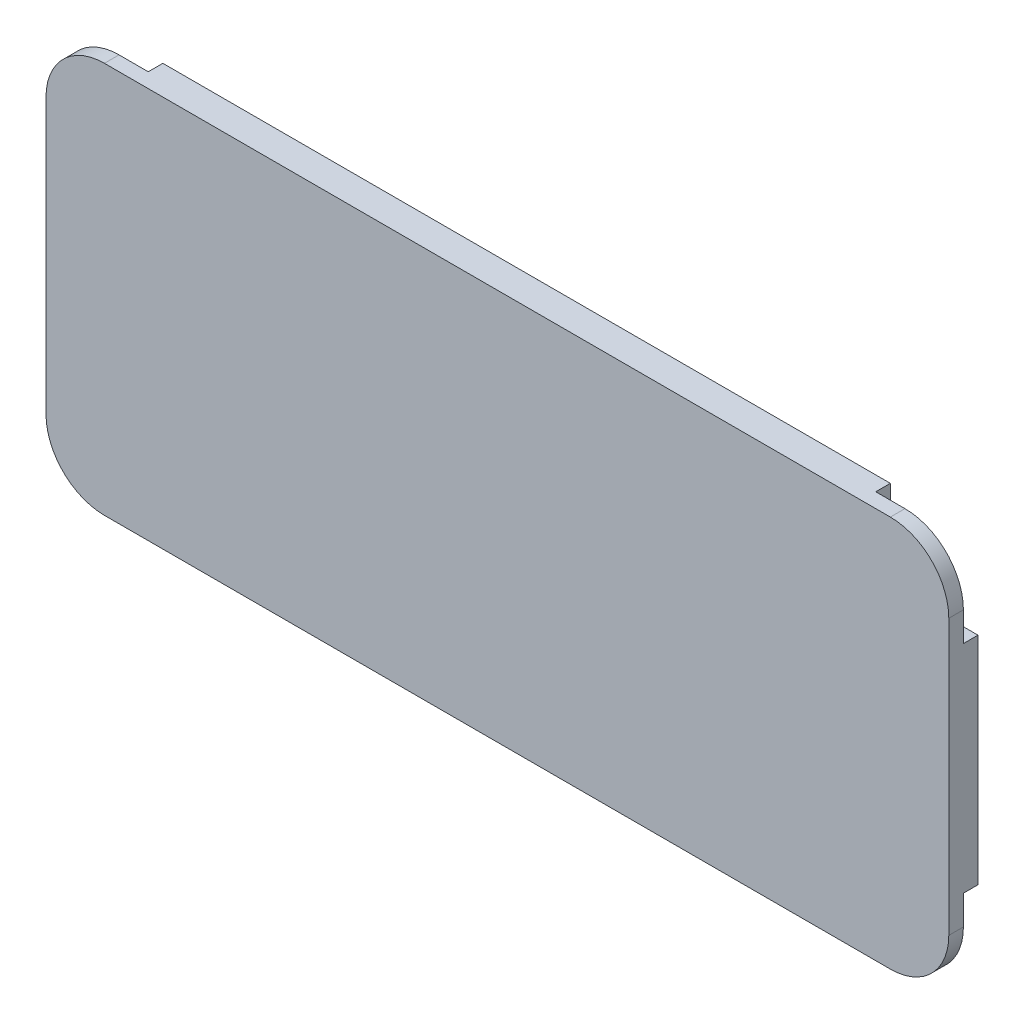
SolidWorks part; units mm, degrees
ref_plane "Front" through (0, 0, 0) normal (0, 0, 1) x (1, 0, 0)
ref_plane "Top" through (0, 0, 0) normal (0, 1, 0) x (1, 0, 0)
ref_plane "Right" through (0, 0, 0) normal (1, 0, 0) x (0, 0, -1)
sketch "草图1" plane through (0, 0, 0) normal (0, 0, 1) x (1, 0, 0)
  line L1 (2, 0) -> (28.9, 0)
  line L2 (0, 2) -> (0, 11.4)
  line L3 (2, 13.4) -> (28.9, 13.4)
  line L4 (30.9, 2) -> (30.9, 11.4)
  arc A0 (0, 11.4) -> (2, 13.4) centre (2, 11.4) cw
  arc A1 (28.9, 13.4) -> (30.9, 11.4) centre (28.9, 11.4) cw
  arc A2 (28.9, 0) -> (30.9, 2) centre (28.9, 2) ccw
  arc A3 (2, 0) -> (0, 2) centre (2, 2) cw
  point P7 (0, 13.4)
  point P12 (30.9, 0)
  point P15 (0, 0)
  dimension "D3" = 2
  dimension "D1" = 30.9
  dimension "D2" = 13.4
extrude "凸台-拉伸1" add sketch "草图1" along normal blind 1
sketch "草图3" plane through (0, 0, 0) normal (0, 0, -1) x (-1, 0, 0)
  line L0 (-1030.9, 6.7) -> (48969.1, 6.7) construction
  line L5 (-30.9, 13.4) -> (-27.9, 13.4)
  line L6 (-30.9, 13.4) -> (-30.9, 10.4)
  line L7 (-30.9, 10.4) -> (-28.4, 10.4)
  line L8 (-27.9, 13.4) -> (-27.9, 10.9)
  line L9 (-30.9, 2) -> (-30.9, 11.4) construction
  line L10 (-15.45, -986.6) -> (-15.45, 49013.4) construction
  line L11 (-28.9, 13.4) -> (-2, 13.4) construction
  line L12 (-3, 13.4) -> (-3, 10.9)
  line L13 (0, 10.4) -> (-2.5, 10.4)
  line L14 (0, 13.4) -> (0, 10.4)
  line L15 (0, 13.4) -> (-3, 13.4)
  line L16 (0, 0) -> (-3, 0)
  line L17 (0, 0) -> (0, 3)
  line L18 (0, 3) -> (-2.5, 3)
  line L19 (-3, 0) -> (-3, 2.5)
  line L20 (-27.9, 0) -> (-27.9, 2.5)
  line L21 (-30.9, 3) -> (-28.4, 3)
  line L22 (-30.9, 0) -> (-30.9, 3)
  line L23 (-30.9, 0) -> (-27.9, 0)
  arc A0 (-28.4, 10.4) -> (-27.9, 10.9) centre (-28.4, 10.9) ccw
  arc A1 (-2.5, 10.4) -> (-3, 10.9) centre (-2.5, 10.9) cw
  arc A2 (-2.5, 3) -> (-3, 2.5) centre (-2.5, 2.5) ccw
  arc A3 (-28.4, 3) -> (-27.9, 2.5) centre (-28.4, 2.5) cw
  point P11 (-30.9, 6.7)
  point P16 (-15.45, 13.4)
  dimension "D2" = 3
  dimension "D3" = 0.5
  dimension "D1" = 3
extrude "切除-拉伸2" cut sketch "草图3" against normal blind 0.5
